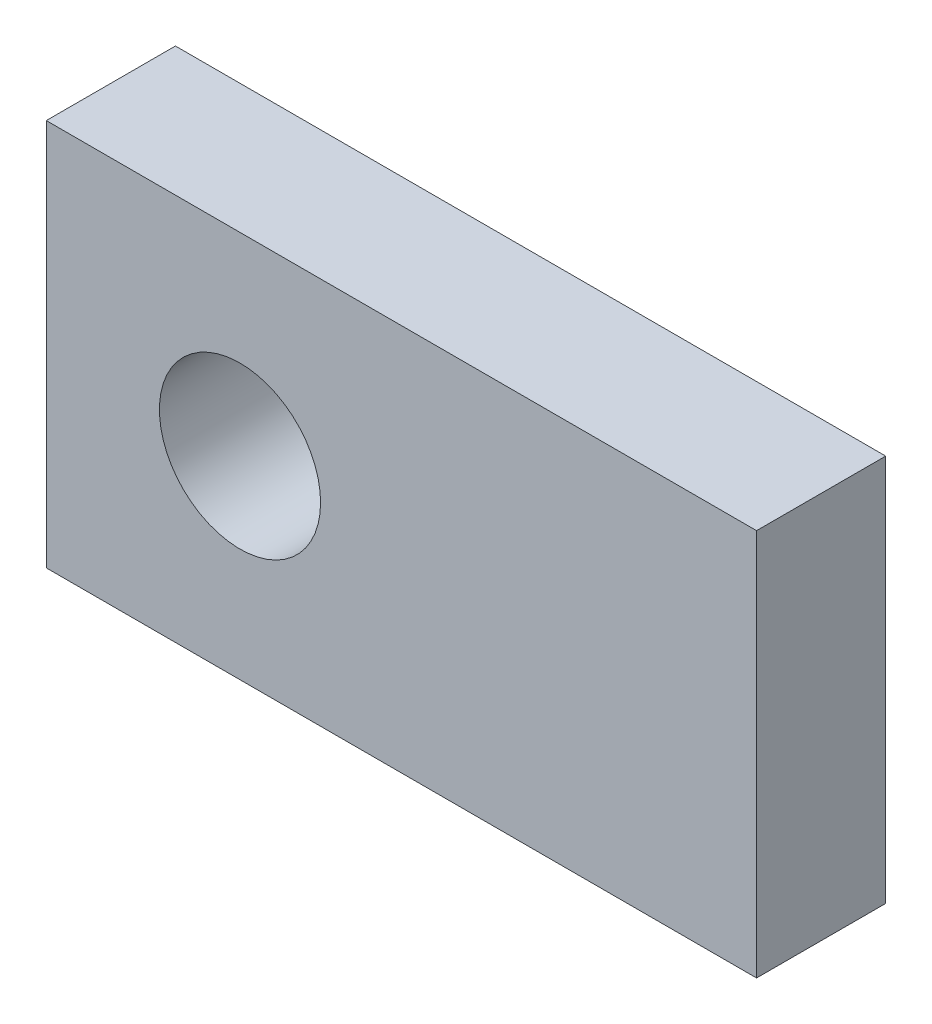
SolidWorks part; units mm, degrees
ref_plane "Front Plane" through (0, 0, 0) normal (0, 0, 1) x (1, 0, 0)
ref_plane "Top Plane" through (0, 0, 0) normal (0, 1, 0) x (1, 0, 0)
ref_plane "Right Plane" through (0, 0, 0) normal (1, 0, 0) x (0, 0, -1)
sketch "Sketch1" plane through (0, 0, 0) normal (0, 0, 1) x (1, 0, 0)
  line L1 (-9.525, 9.525) -> (25.4, 9.525)
  line L2 (-9.525, 9.525) -> (-9.525, -9.525)
  line L3 (-9.525, -9.525) -> (25.4, -9.525)
  line L4 (25.4, 9.525) -> (25.4, -9.525)
  circle A0 centre (0, 0) radius 3.9624
  dimension "D1" = 7.9248
  dimension "D2" = 9.525
  dimension "D3" = 9.525
  dimension "D4" = 19.05
  dimension "D5" = 34.925
extrude "Boss-Extrude1" add sketch "Sketch1" along normal blind 6.35
